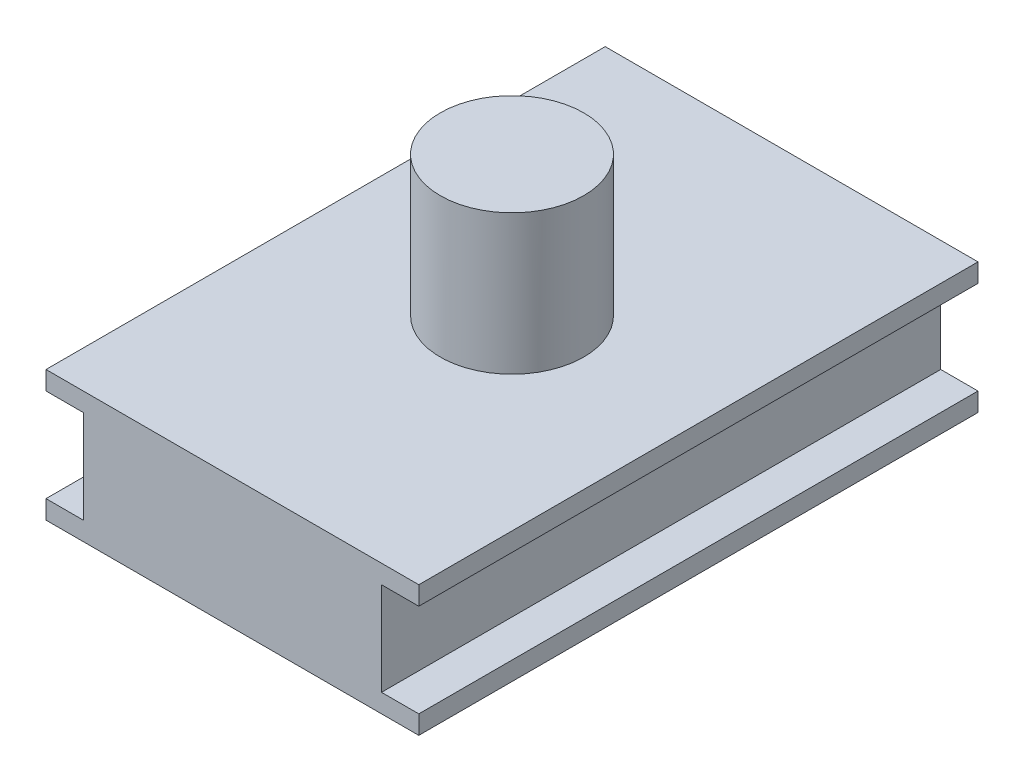
SolidWorks part; units mm, degrees
ref_plane "Front Plane" through (0, 0, 0) normal (0, 0, 1) x (1, 0, 0)
ref_plane "Top Plane" through (0, 0, 0) normal (0, 1, 0) x (1, 0, 0)
ref_plane "Right Plane" through (0, 0, 0) normal (1, 0, 0) x (0, 0, -1)
sketch "Sketch1" plane through (0, 0, 0) normal (0, 1, 0) x (1, 0, 0)
  line L1 (-10, -15) -> (10, -15)
  line L2 (-10, -15) -> (-10, 15)
  line L3 (-10, 15) -> (10, 15)
  line L4 (10, -15) -> (10, 15)
  line L5 (-10, -15) -> (10, 15) construction
  line L6 (-10, 15) -> (10, -15) construction
  point P0 (0, 0)
  dimension "D1" = 20
  dimension "D2" = 30
extrude "Boss-Extrude1" add sketch "Sketch1" along normal blind 7
sketch "Sketch2" plane through (10, 0, 0) normal (1, 0, 0) x (0, 0, -1)
  line L0 (15, 7) -> (15, 0) construction
  line L1 (-15, 1) -> (15, 1)
  line L2 (-15, 1) -> (-15, 6)
  line L3 (-15, 6) -> (15, 6)
  line L4 (15, 1) -> (15, 6)
  line L5 (-15, 1) -> (15, 6) construction
  line L6 (-15, 6) -> (15, 1) construction
  line L7 (-15, 7) -> (15, 7) construction
  line L8 (-15, 0) -> (15, 0) construction
  point P0 (0, 3.5)
  dimension "D1" = 1
  dimension "D2" = 1
extrude "Cut-Extrude1" cut sketch "Sketch2" against normal blind 2
sketch "Sketch3" plane through (-10, 0, 0) normal (-1, 0, 0) x (0, 0, 1)
  line L0 (15, 7) -> (15, 0) construction
  line L1 (-15, 1) -> (15, 1)
  line L2 (-15, 1) -> (-15, 6)
  line L3 (-15, 6) -> (15, 6)
  line L4 (15, 1) -> (15, 6)
  line L5 (-15, 1) -> (15, 6) construction
  line L6 (-15, 6) -> (15, 1) construction
  line L7 (-15, 7) -> (15, 7) construction
  line L8 (-15, 0) -> (15, 0) construction
  point P0 (0, 3.5)
  dimension "D1" = 1
  dimension "D2" = 1
extrude "Cut-Extrude2" cut sketch "Sketch3" against normal blind 2
sketch "Sketch4" plane through (0, 7, 0) normal (0, 1, 0) x (1, 0, 0)
  circle A0 centre (0, 0) radius 3.85
  dimension "D1" = 7.7
extrude "Boss-Extrude2" add sketch "Sketch4" along normal blind 7.5
